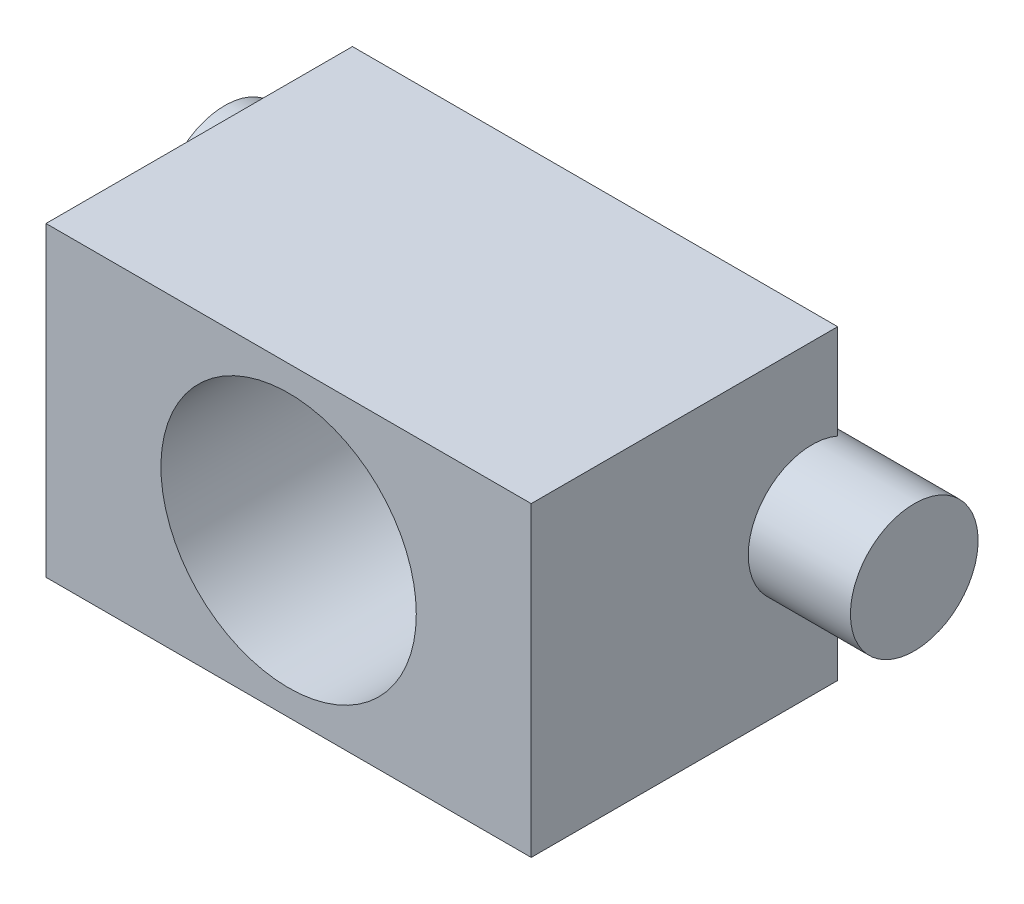
SolidWorks part; units mm, degrees
ref_plane "Front Plane" through (0, 0, 0) normal (0, 0, 1) x (1, 0, 0)
ref_plane "Top Plane" through (0, 0, 0) normal (0, 1, 0) x (1, 0, 0)
ref_plane "Right Plane" through (0, 0, 0) normal (1, 0, 0) x (0, 0, -1)
sketch "Sketch1" plane through (0, 0, 0) normal (0, 0, 1) x (1, 0, 0)
  line L1 (0, 0) -> (95, 0)
  line L2 (0, 0) -> (0, 60)
  line L3 (0, 60) -> (95, 60)
  line L4 (95, 0) -> (95, 60)
  circle A0 centre (47.5, 30) radius 25
  point P7 (47.5, 0)
  point P8 (0, 0)
  point P9 (0, 30)
  dimension "D1" = 60
  dimension "D3" = 50
  dimension "D2" = 95
extrude "Boss-Extrude1" add sketch "Sketch1" along normal blind 60
sketch "Sketch2" plane through (0, 0, 0) normal (-1, 0, 0) x (0, 0, 1)
  line L0 (60, 60) -> (60, 0) construction
  line L1 (0, 60) -> (0, 0) construction
  circle A0 centre (5, 30) radius 12.5
  point P4 (0, 0)
  point P7 (0, 30)
  dimension "D2" = 25
  dimension "D1" = 55
extrude "Boss-Extrude2" add sketch "Sketch2" along normal blind 20 and the other way blind 115
